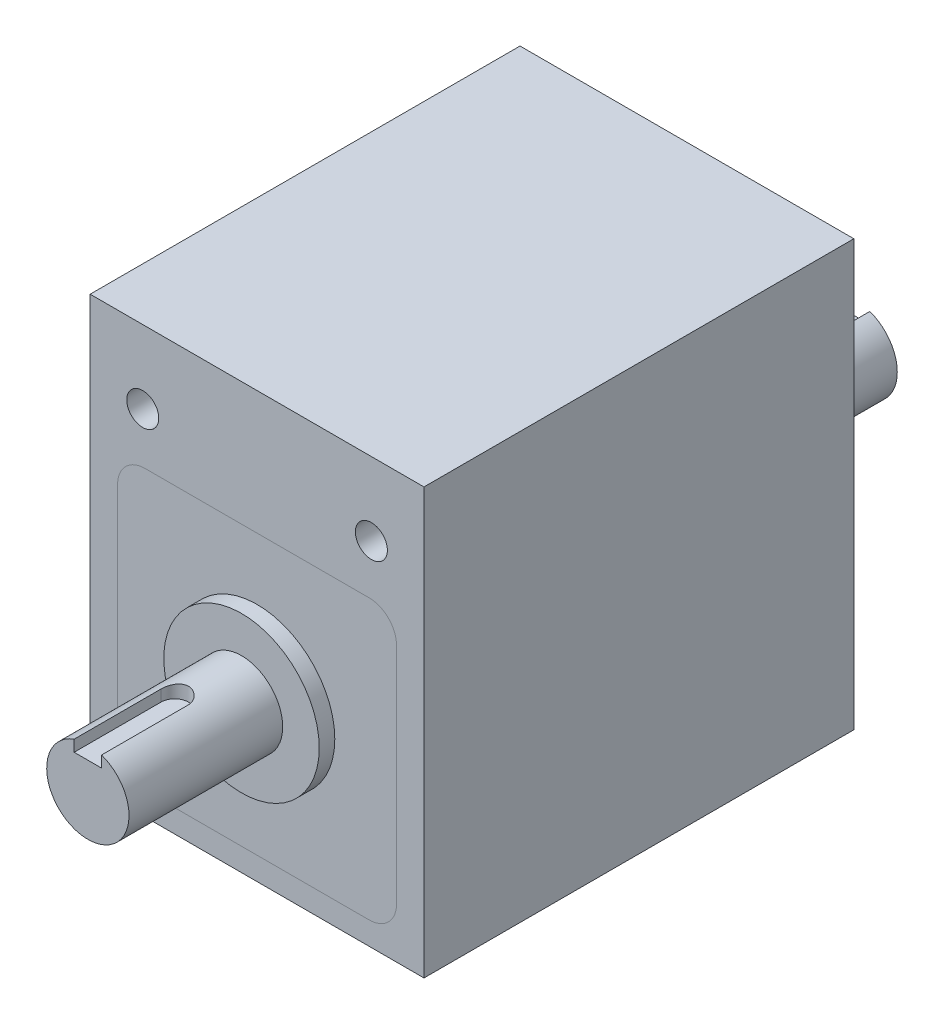
SolidWorks part; units mm, degrees
ref_plane "Front" through (0, 0, 0) normal (0, 0, 1) x (1, 0, 0)
ref_plane "Top" through (0, 0, 0) normal (0, 1, 0) x (1, 0, 0)
ref_plane "Right" through (0, 0, 0) normal (1, 0, 0) x (0, 0, -1)
sketch "Sketch1" plane through (0, 0, 0) normal (0, 0, 1) x (1, 0, 0)
  line L0 (0, 0) -> (0, 11) construction
  line L1 (-36.5, 57.5) -> (36.5, 57.5)
  line L2 (-36.5, 57.5) -> (-36.5, -35.5)
  line L3 (-36.5, -35.5) -> (36.5, -35.5)
  line L4 (36.5, 57.5) -> (36.5, -35.5)
  line L5 (-36.5, 57.5) -> (36.5, -35.5) construction
  line L6 (-36.5, -35.5) -> (36.5, 57.5) construction
  point P0 (0, 11)
  dimension "D1" = 35.5
  dimension "D2" = 93
  dimension "D3" = 73
extrude "Boss-Extrude1" add sketch "Sketch1" along normal mid plane 94
sketch "Sketch2" plane through (0, 0, 47) normal (0, 0, 1) x (1, 0, 0)
  circle A0 centre (0, 0) radius 17
  dimension "D1" = 34
extrude "Boss-Extrude2" add sketch "Sketch2" along normal blind 3.4
sketch "Sketch3" plane through (0, 0, 50.4) normal (0, 0, 1) x (1, 0, 0)
  circle A0 centre (0, 0) radius 9
  dimension "D1" = 18
extrude "Boss-Extrude3" add sketch "Sketch3" along normal blind 33.6
sketch "Sketch9" plane through (0, 0, 47) normal (0, 0, 1) x (1, 0, 0)
  line L0 (36.5, -35.5) -> (36.5, 57.5) construction
  line L1 (-24.5, -30.5) -> (24.5, -30.5)
  line L2 (-30.5, -24.5) -> (-30.5, 24.5)
  line L3 (-24.5, 30.5) -> (24.5, 30.5)
  line L4 (30.5, -24.5) -> (30.5, 24.5)
  line L5 (-30.5, -30.5) -> (30.5, 30.5) construction
  line L6 (-30.5, 30.5) -> (30.5, -30.5) construction
  arc A0 (-24.5, -30.5) -> (-30.5, -24.5) centre (-24.5, -24.5) cw
  arc A1 (24.5, -30.5) -> (30.5, -24.5) centre (24.5, -24.5) ccw
  arc A2 (24.5, 30.5) -> (30.5, 24.5) centre (24.5, 24.5) cw
  arc A3 (-30.5, 24.5) -> (-24.5, 30.5) centre (-24.5, 24.5) cw
  point P0 (0, 0)
  dimension "D2" = 6
  dimension "D1" = 6
split line "Split Line1"
sketch "Sketch10" plane through (0, 0, -47) normal (0, 0, -1) x (-1, 0, 0)
  line L12 (-24.5, -30.5) -> (24.5, -30.5)
  line L13 (-30.5, 24.5) -> (-30.5, -24.5)
  line L14 (24.5, 30.5) -> (-24.5, 30.5)
  line L15 (30.5, -24.5) -> (30.5, 24.5)
  line L16 (-24.5, -30.5) -> (24.5, -30.5)
  line L17 (-30.5, 24.5) -> (-30.5, -24.5)
  line L18 (24.5, 30.5) -> (-24.5, 30.5)
  line L19 (30.5, -24.5) -> (30.5, 24.5)
  arc A4 (24.5, -30.5) -> (30.5, -24.5) centre (24.5, -24.5) ccw
  arc A5 (-30.5, -24.5) -> (-24.5, -30.5) centre (-24.5, -24.5) ccw
  arc A6 (-24.5, 30.5) -> (-30.5, 24.5) centre (-24.5, 24.5) ccw
  arc A7 (30.5, 24.5) -> (24.5, 30.5) centre (24.5, 24.5) ccw
  arc A8 (24.5, -30.5) -> (30.5, -24.5) centre (24.5, -24.5) ccw
  arc A9 (-30.5, -24.5) -> (-24.5, -30.5) centre (-24.5, -24.5) ccw
  arc A10 (-24.5, 30.5) -> (-30.5, 24.5) centre (-24.5, 24.5) ccw
  arc A11 (30.5, 24.5) -> (24.5, 30.5) centre (24.5, 24.5) ccw
  dimension "D2" = 0
split line "Split Line2"
ref_plane "Plane1" through (0, 9, 0) normal (0, 1, 0) x (1, 0, 0)
sketch "Sketch4" plane through (0, 9, 0) normal (0, 1, 0) x (1, 0, 0)
  line L0 (0, -84) -> (0, -73) construction
  line L1 (-9, -84) -> (9, -84) construction
  line L3 (-3, -62) -> (3, -62)
  line L4 (-3, -62) -> (-3, -84)
  line L5 (-3, -84) -> (3, -84)
  line L6 (3, -62) -> (3, -84)
  line L7 (-3, -62) -> (3, -84) construction
  line L8 (-3, -84) -> (3, -62) construction
  circle A0 centre (0, -65) radius 3
  dimension "D1" = 6
  dimension "D2" = 22
extrude "Cut-Extrude1" cut sketch "Sketch4" against normal blind 3 contours A0 L4 L5 L6 | A0
sketch "Sketch5" plane through (0, 0, 47) normal (0, 0, 1) x (1, 0, 0)
  line L0 (0, 0) -> (0, 41.5) construction
  line L1 (-25, 41.5) -> (25, 41.5) construction
  line L3 (36.5, 57.5) -> (-36.5, 57.5) construction
  point P7 (0, 41.5)
  dimension "D1" = 50
  dimension "D2" = 16
hole_wizard "M8x1.0 Tapped Hole1" positions "3DSketch1" profile "Sketch6" tap size "M8x1.0" standard "ANSI Metric"
sketch3d "3DSketch1"
  point P0 (-25, 41.5, 47)
  point P3 (25, 41.5, 47)
sketch "Sketch6" plane through (-25, 41.5, 47) normal (1, 0, 0) x (0, -1, 0)
  line L0 (0, 0) -> (0, 10.103)
  line L1 (0, 10.103) -> (3.5, 8)
  line L2 (3.5, 8) -> (3.5, 0)
  line L5 (3.5, 0) -> (0, 0)
  line L10 (0, 10.103) -> (-3.5, 8) construction
  line L11 (0, -6.35) -> (0, 107.95) construction
  dimension "Tap Drill Dia." = 7
  dimension "Tap Drill Depth" = 8
  dimension "Drill Angle" = 118
cosmetic thread "Hole Thread1" parameters "D1"=8, "D2"=8
cosmetic thread "Hole Thread2" parameters "D1"=8, "D2"=8
mirror "Mirror1" about plane through (0, 0, 0) normal (0, 0, 1) of "M8x1.0 Tapped Hole1", "Cut-Extrude1", "Boss-Extrude3", "Boss-Extrude2"
cosmetic thread "Hole Thread3" parameters "D1"=8, "D2"=8
cosmetic thread "Hole Thread4" parameters "D1"=8, "D2"=8
sketch "Sketch7" plane through (0, -35.5, 0) normal (0, -1, 0) x (1, 0, 0)
  line L1 (-26.5, -26.5) -> (26.5, -26.5) construction
  line L2 (-26.5, -26.5) -> (-26.5, 26.5) construction
  line L3 (-26.5, 26.5) -> (26.5, 26.5) construction
  line L4 (26.5, -26.5) -> (26.5, 26.5) construction
  line L5 (-26.5, -26.5) -> (26.5, 26.5) construction
  line L6 (-26.5, 26.5) -> (26.5, -26.5) construction
  point P0 (0, 0)
  dimension "D1" = 53
  dimension "D2" = 53
hole_wizard "M8x1.0 Tapped Hole2" positions "3DSketch2" profile "Sketch8" tap size "M8x1.0" standard "ANSI Metric"
sketch3d "3DSketch2"
  point P0 (26.5, -35.5, 26.5)
  point P3 (26.5, -35.5, -26.5)
  point P6 (-26.5, -35.5, -26.5)
  point P9 (-26.5, -35.5, 26.5)
sketch "Sketch8" plane through (26.5, -35.5, 26.5) normal (1, 0, 0) x (0, 0, -1)
  line L0 (0, 0) -> (0, 21.103)
  line L1 (0, 21.103) -> (3.5, 19)
  line L2 (3.5, 19) -> (3.5, 0)
  line L5 (3.5, 0) -> (0, 0)
  line L10 (0, 21.103) -> (-3.5, 19) construction
  line L11 (0, -6.35) -> (0, 107.95) construction
  dimension "Tap Drill Dia." = 7
  dimension "Tap Drill Depth" = 19
  dimension "Drill Angle" = 118
cosmetic thread "Hole Thread5" parameters "D1"=16, "D2"=8
cosmetic thread "Hole Thread6" parameters "D1"=16, "D2"=8
cosmetic thread "Hole Thread7" parameters "D1"=16, "D2"=8
cosmetic thread "Hole Thread8" parameters "D1"=16, "D2"=8
